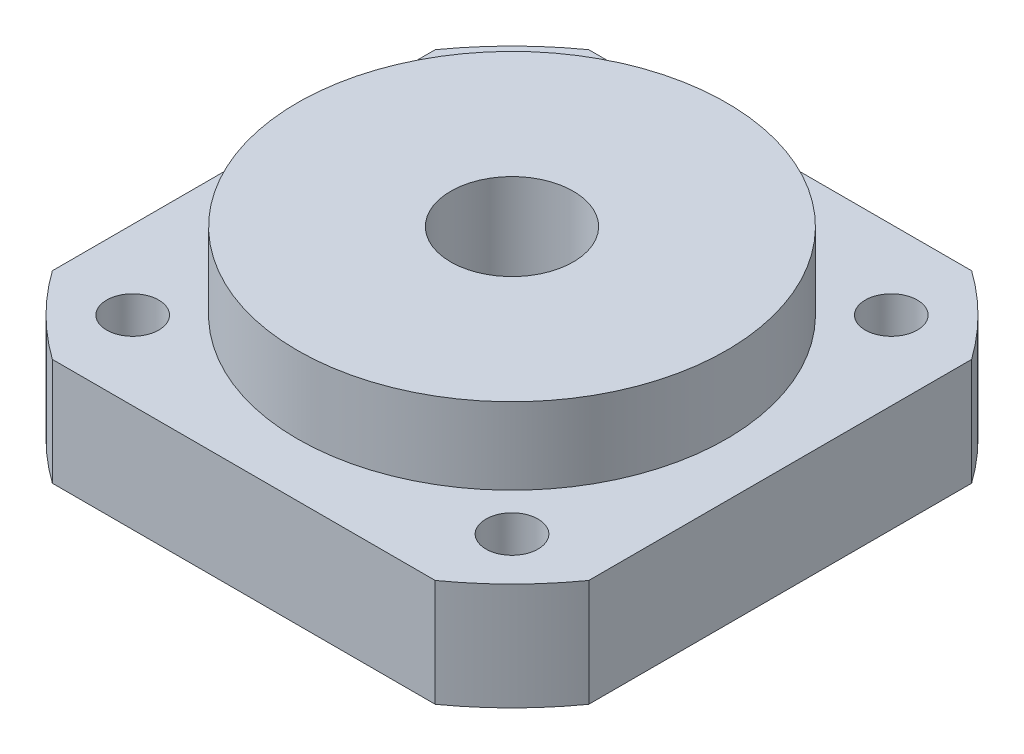
SolidWorks part; units mm, degrees
ref_plane "Спереди" through (0, 0, 0) normal (0, 0, 1) x (1, 0, 0)
ref_plane "Сверху" through (0, 0, 0) normal (0, 1, 0) x (1, 0, 0)
ref_plane "Справа" through (0, 0, 0) normal (1, 0, 0) x (0, 0, -1)
sketch "Эскиз5" plane through (0, 0, 0) normal (0, 1, 0) x (1, 0, 0)
  line L1 (-12.49, -17.5) -> (12.49, -17.5)
  line L2 (-17.5, -12.49) -> (-17.5, 12.49)
  line L3 (-12.49, 17.5) -> (12.49, 17.5)
  line L4 (17.5, -12.49) -> (17.5, 12.49)
  circle A0 centre (0, 0) radius 4
  circle A1 centre (0, 0) radius 17.5 construction
  circle A2 centre (-12.3744, 12.3744) radius 1.7
  circle A3 centre (12.3744, 12.3744) radius 1.7
  circle A4 centre (12.3744, -12.3744) radius 1.7
  circle A5 centre (-12.3744, -12.3744) radius 1.7
  arc A6 (-12.49, 17.5) -> (-17.5, 12.49) centre (0, 0) ccw
  arc A7 (17.5, 12.49) -> (12.49, 17.5) centre (0, 0) ccw
  arc A8 (12.49, -17.5) -> (17.5, -12.49) centre (0, 0) ccw
  arc A9 (-17.5, -12.49) -> (-12.49, -17.5) centre (0, 0) ccw
  point P0 (0, 0)
  point P27 (0, 0)
  dimension "D2" = 8
  dimension "D3" = 35
  dimension "D4" = 3.4
  dimension "D5" = 3.4
  dimension "D6" = 3.4
  dimension "D7" = 3.4
  dimension "D8" = 43
extrude "Бобышка-Вытянуть2" add sketch "Эскиз5" along normal blind 12
sketch "Эскиз7" plane through (0, 12, 0) normal (0, 1, 0) x (1, 0, 0)
  line L1 (-17.5, 17.5) -> (17.5, 17.5)
  line L2 (-17.5, 17.5) -> (-17.5, -17.5)
  line L3 (-17.5, -17.5) -> (17.5, -17.5)
  line L4 (17.5, 17.5) -> (17.5, -17.5)
  line L5 (-17.5, 17.5) -> (17.5, -17.5) construction
  line L6 (-17.5, -17.5) -> (17.5, 17.5) construction
  circle A0 centre (0, 0) radius 14
  dimension "D1" = 28
  dimension "D2" = 35
extrude "Вырез-Вытянуть4" cut sketch "Эскиз7" against normal blind 5
sketch "Эскиз8" plane through (0, 0, 0) normal (0, -1, 0) x (1, 0, 0)
  circle A0 centre (-12.3744, 12.3744) radius 3.25
  circle A1 centre (12.3744, 12.3744) radius 3.25
  circle A2 centre (12.3744, -12.3744) radius 3.25
  circle A3 centre (-12.3744, -12.3744) radius 3.25
  dimension "D1" = 6.5
  dimension "D2" = 6.5
  dimension "D3" = 6.5
  dimension "D4" = 6.5
extrude "Вырез-Вытянуть5" cut sketch "Эскиз8" against normal blind 4
